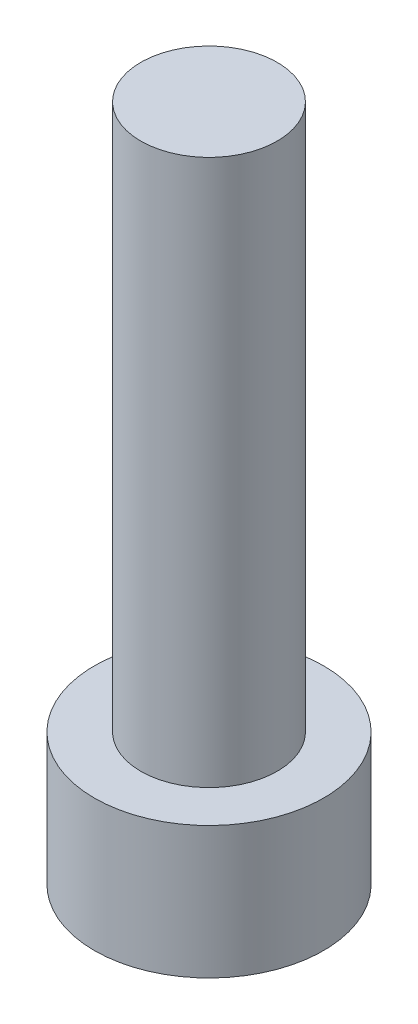
SolidWorks part; units mm, degrees
ref_plane "前视基准面" through (0, 0, 0) normal (0, 0, 1) x (1, 0, 0)
ref_plane "上视基准面" through (0, 0, 0) normal (0, 1, 0) x (1, 0, 0)
ref_plane "右视基准面" through (0, 0, 0) normal (1, 0, 0) x (0, 0, -1)
sketch "草图1" plane through (0, 0, 0) normal (0, 1, 0) x (1, 0, 0)
  circle A0 centre (0, 0) radius 4.2
extrude "凸台-拉伸1" add sketch "草图1" along normal blind 4.84
sketch "草图2" plane through (0, 4.84, 0) normal (0, 1, 0) x (1, 0, 0)
  circle A0 centre (0, 0) radius 2.5
extrude "凸台-拉伸2" add sketch "草图2" along normal blind 20
sketch "草图3" plane through (0, 0, 0) normal (0, -1, 0) x (1, 0, 0)
  line L1 (2.3, 0) -> (1.15, 1.9919)
  line L2 (1.15, 1.9919) -> (-1.15, 1.9919)
  line L3 (-1.15, 1.9919) -> (-2.3, 0)
  line L4 (-2.3, 0) -> (-1.15, -1.9919)
  line L5 (-1.15, -1.9919) -> (1.15, -1.9919)
  line L6 (1.15, -1.9919) -> (2.3, 0)
  circle A0 centre (0, 0) radius 1.9919 construction
extrude "切除-拉伸1" cut sketch "草图3" against normal blind 3.4
